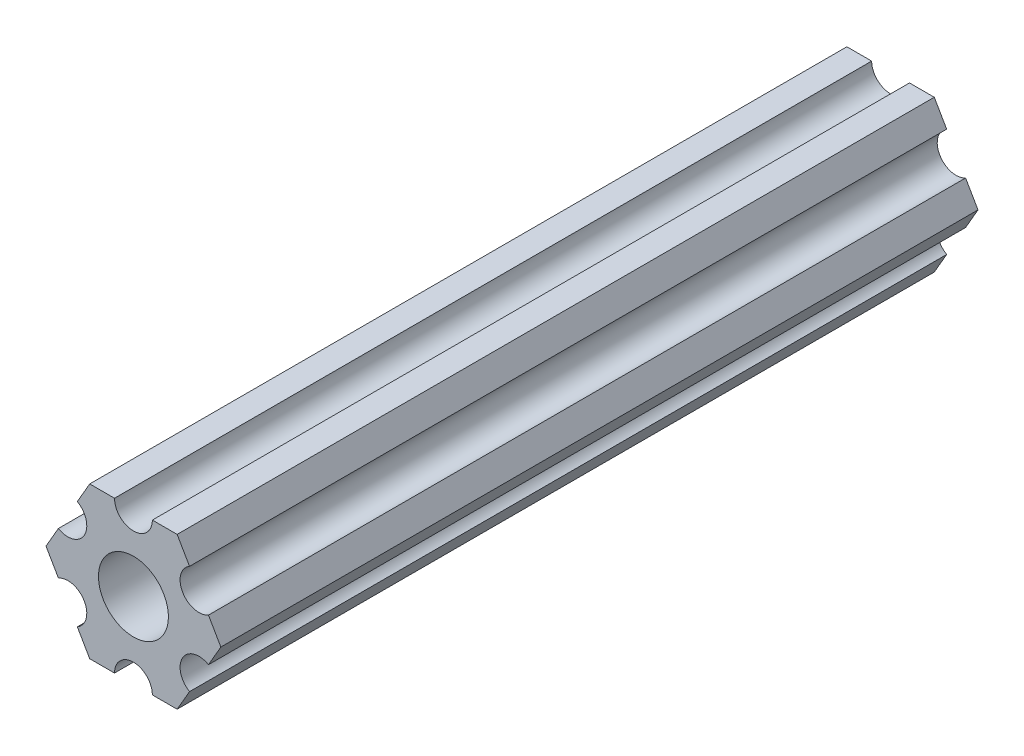
SolidWorks part; units mm, degrees
ref_plane "Front Plane" through (0, 0, 0) normal (0, 0, 1) x (1, 0, 0)
ref_plane "Top Plane" through (0, 0, 0) normal (0, 1, 0) x (1, 0, 0)
ref_plane "Right Plane" through (0, 0, 0) normal (1, 0, 0) x (0, 0, -1)
ref_plane "Plane1" through (0, 0, 0) normal (0, 0, -1) x (-1, 0, 0)
sketch "Sketch1" plane through (0, 0, 0) normal (0, 0, -1) x (-1, 0, 0)
  line L0 (-7.3323, 0) -> (-6.293, -1.8002)
  line L1 (-4.7055, -4.5498) -> (-3.6662, -6.35)
  line L2 (-3.6662, -6.35) -> (-1.5875, -6.35)
  line L3 (1.5875, -6.35) -> (3.6662, -6.35)
  line L4 (3.6662, -6.35) -> (4.7055, -4.5498)
  line L5 (6.293, -1.8002) -> (7.3323, 0)
  line L6 (7.3323, 0) -> (6.293, 1.8002)
  line L7 (4.7055, 4.5498) -> (3.6662, 6.35)
  line L8 (3.6662, 6.35) -> (1.5875, 6.35)
  line L9 (-1.5875, 6.35) -> (-3.6662, 6.35)
  line L10 (-3.6662, 6.35) -> (-4.7055, 4.5498)
  line L11 (-6.293, 1.8002) -> (-7.3323, 0)
  circle A0 centre (0, 0) radius 2.9337
  arc A1 (-6.293, -1.8002) -> (-4.7055, -4.5498) centre (-5.4993, -3.175) cw
  arc A2 (-1.5875, -6.35) -> (1.5875, -6.35) centre (0, -6.35) cw
  arc A3 (4.7055, -4.5498) -> (6.293, -1.8002) centre (5.4993, -3.175) cw
  arc A4 (6.293, 1.8002) -> (4.7055, 4.5498) centre (5.4993, 3.175) cw
  arc A5 (1.5875, 6.35) -> (-1.5875, 6.35) centre (0, 6.35) cw
  arc A6 (-4.7055, 4.5498) -> (-6.293, 1.8002) centre (-5.4993, 3.175) cw
extrude "Boss-Extrude1" add sketch "Sketch1" against normal blind 63.5
